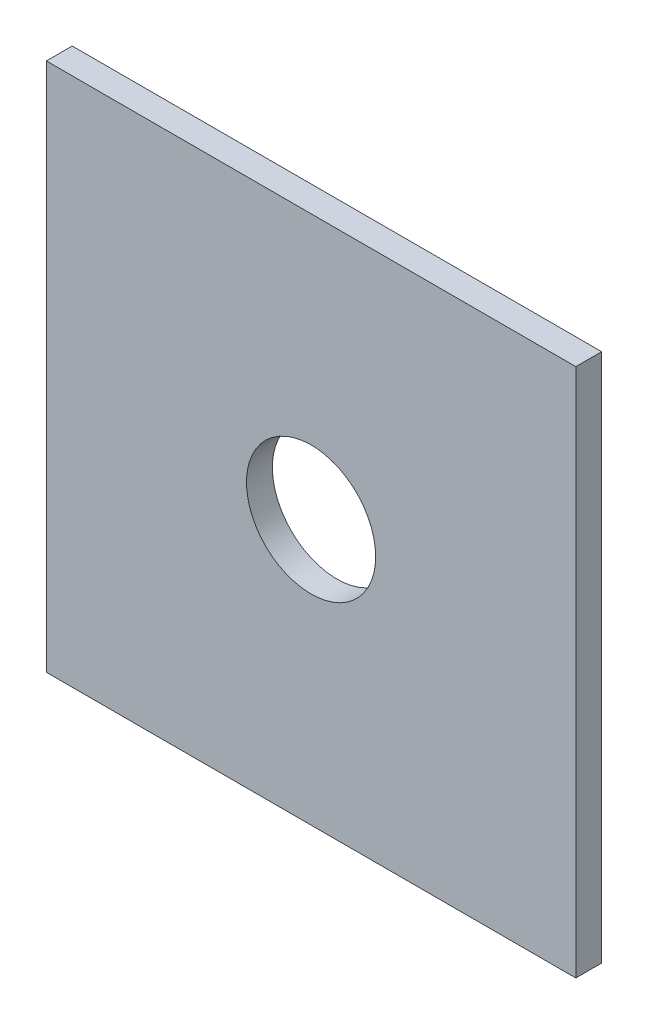
SolidWorks part; units mm, degrees
ref_plane "Front Plane" through (0, 0, 0) normal (0, 0, 1) x (1, 0, 0)
ref_plane "Top Plane" through (0, 0, 0) normal (0, 1, 0) x (1, 0, 0)
ref_plane "Right Plane" through (0, 0, 0) normal (1, 0, 0) x (0, 0, -1)
sketch "Sketch1" plane through (0, 0, 0) normal (0, 0, 1) x (1, 0, 0)
  line L1 (75, -223) -> (34, -223)
  line L2 (75, -223) -> (75, -182)
  line L3 (75, -182) -> (34, -182)
  line L4 (34, -223) -> (34, -182)
  dimension "D1" = 41
extrude "Boss-Extrude1" add sketch "Sketch1" along normal blind 2
sketch "Sketch2" plane through (0, 0, 0) normal (0, 0, 1) x (1, 0, 0)
  line L0 (34, -182) -> (75, -223) construction
  line L1 (34, -223) -> (75, -182) construction
  circle A0 centre (54.5, -202.5) radius 5
extrude "Cut-Extrude2" cut sketch "Sketch2" along normal through all contours A0
equation "\"x\"= 10'hole for stepper"
equation "\"D1@Sketch2\"=\"x\""
